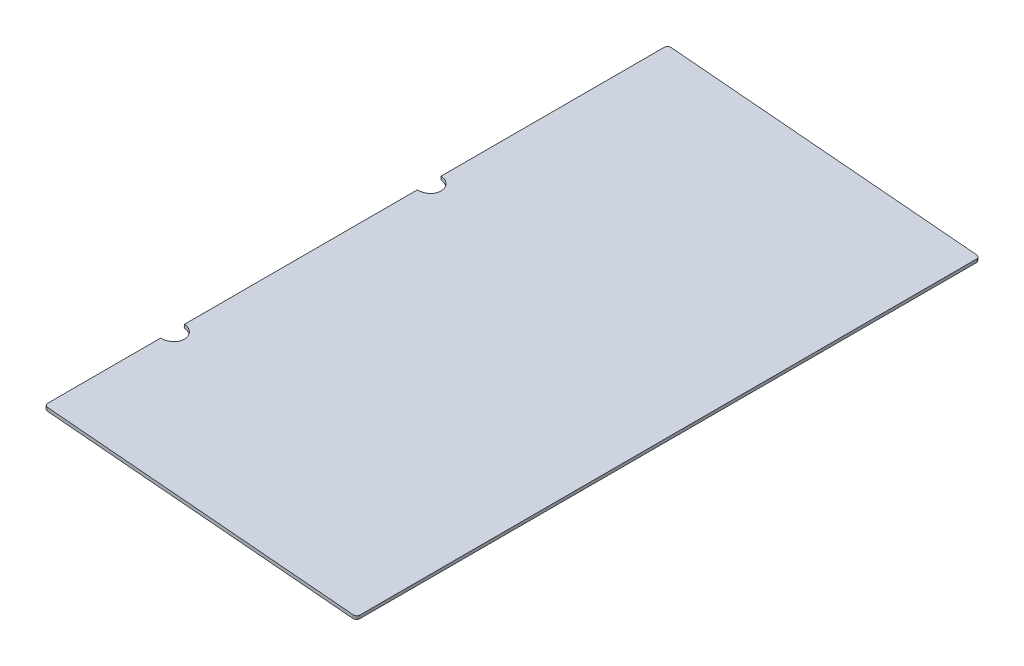
SolidWorks part; units mm, degrees
material "PC High Viscosity"
ref_plane "Front Plane" through (0, 0, 0) normal (0, 0, 1) x (1, 0, 0)
ref_plane "Top Plane" through (0, 0, 0) normal (0, 1, 0) x (1, 0, 0)
ref_plane "Right Plane" through (0, 0, 0) normal (1, 0, 0) x (0, 0, -1)
sketch "Sketch1" plane through (0, 0, 0) normal (0, 0, 1) x (1, 0, 0)
  line L0 (0, 44.45) -> (44.45, 44.45) construction
  line L1 (0, 0) -> (44.45, 0) construction
  line L2 (0, 0) -> (0, 44.45) construction
  line L3 (0, 44.45) -> (44.45, 44.45) construction
  line L4 (44.45, 0) -> (44.45, 44.45) construction
  line L5 (44.8651, 44.4319) -> (115.0456, 38.2919) construction
  line L6 (115.0456, 38.2919) -> (115.4607, 43.0363) construction
  line L7 (115.4607, 43.0363) -> (45.2802, 49.1763) construction
  line L8 (44.45, 49.2125) -> (0, 49.2125) construction
  line L9 (0, 49.2125) -> (0, 44.45) construction
  line L10 (22.225, 51.1933) -> (607.3673, 0)
  line L12 (607.9208, 6.3258) -> (22.7784, 57.5192)
  line L13 (22.7784, 57.5192) -> (22.225, 51.1933)
  line L14 (607.3673, 0) -> (607.9208, 6.3258)
  arc A0 (44.8651, 44.4319) -> (44.45, 44.45) centre (44.45, 39.6875) ccw construction
  arc A1 (45.2802, 49.1763) -> (44.45, 49.2125) centre (44.45, 39.6875) ccw construction
  point P19 (22.225, 44.45)
  dimension "D3" = 4.7625
  dimension "D4" = 9.525
  dimension "D1" = 44.45
  dimension "D2" = 4.7625
  dimension "D5" = 44.45
  dimension "D6" = 85
  dimension "D7" = 6.35
  dimension "D8" = 587.3775
extrude "Boss-Extrude1" add sketch "Sketch1" along normal blind 1168.4
sketch "Sketch4" plane through (5.1671, 59.06, 0) normal (0.0872, 0.9962, 0) x (0.9962, -0.0872, 0)
  line L0 (17.6786, -1168.4) -> (17.6786, 0) construction
  line L2 (605.0561, -1168.4) -> (17.6786, -1168.4) construction
  circle A0 centre (17.6786, -446.8812) radius 22.225
  circle A1 centre (17.6786, -927.8937) radius 22.225
  dimension "D1" = 44.45
  dimension "D2" = 240.5062
  dimension "D3" = 481.0125
extrude "Cut-Extrude1" cut sketch "Sketch4" against normal through all
fillet "Fillet1" radius 6.35 4 edges at (607.644, 3.1629, 1168.4) (22.5017, 54.3562, 1168.4) (607.644, 3.1629, 0) (22.5017, 54.3562, 0)
